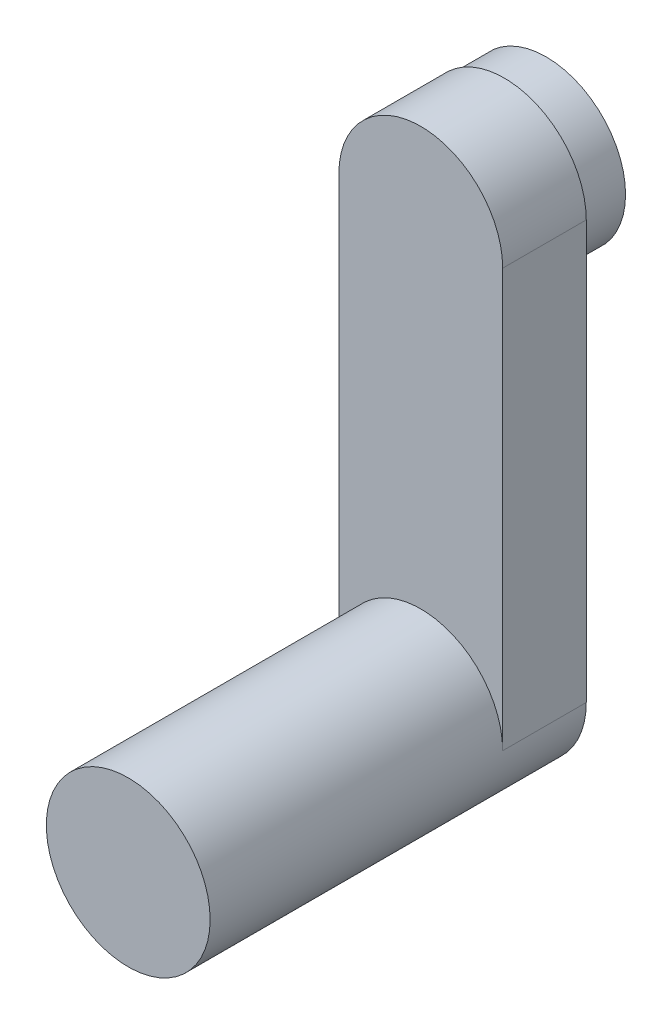
SolidWorks part; units mm, degrees
ref_plane "Front Plane" through (0, 0, 0) normal (0, 0, 1) x (1, 0, 0)
ref_plane "Top Plane" through (0, 0, 0) normal (0, 1, 0) x (1, 0, 0)
ref_plane "Right Plane" through (0, 0, 0) normal (1, 0, 0) x (0, 0, -1)
sketch "Sketch1" plane through (0, 0, 0) normal (0, 0, 1) x (1, 0, 0)
  circle A0 centre (0, 0) radius 49
  dimension "D1" = 98
extrude "Boss-Extrude1" add sketch "Sketch1" along normal blind 175
sketch "Sketch2" plane through (0, 0, 0) normal (0, 0, -1) x (-1, 0, 0)
  line L2 (-49, 0) -> (-49, 250)
  line L4 (49, 0) -> (49, 250)
  arc A0 (-49, 0) -> (49, 0) centre (0, 0) ccw
  circle A1 centre (0, 0) radius 49 construction
  arc A2 (-49, 250) -> (49, 250) centre (0, 250) cw
  dimension "D1" = 250
extrude "Boss-Extrude2" add sketch "Sketch2" along normal blind 50
sketch "Sketch3" plane through (0, 0, -50) normal (0, 0, -1) x (-1, 0, 0)
  circle A0 centre (0, 250) radius 47.5
  circle A1 centre (0, 250) radius 45
  dimension "D1" = 90
  dimension "D2" = 95
extrude "Boss-Extrude3" add sketch "Sketch3" along normal blind 25
